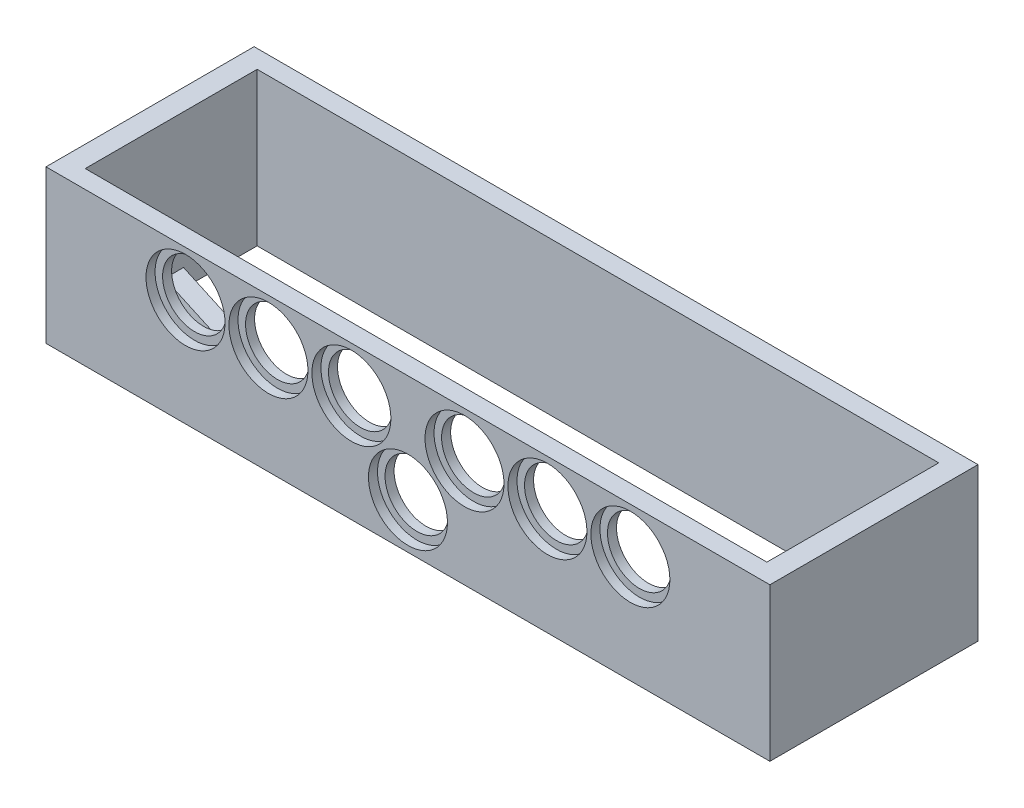
SolidWorks part; units mm, degrees
ref_plane "Přední rovina" through (0, 0, 0) normal (0, 0, 1) x (1, 0, 0)
ref_plane "Horní rovina" through (0, 0, 0) normal (0, 1, 0) x (1, 0, 0)
ref_plane "Pravá rovina" through (0, 0, 0) normal (1, 0, 0) x (0, 0, -1)
sketch "Skica1" plane through (0, 0, 0) normal (0, 1, 0) x (1, 0, 0)
  line L0 (0, 0) -> (240, 0)
  line L1 (240, 0) -> (240, 69)
  line L2 (240, 69) -> (0, 69)
  line L3 (0, 69) -> (0, 0)
  line L4 (7, 63) -> (7, 6)
  line L5 (7, 6) -> (233, 6)
  line L6 (233, 6) -> (233, 63)
  line L7 (233, 63) -> (7, 63)
  dimension "D1" = 240
  dimension "D2" = 69
  dimension "D3" = 6
  dimension "D4" = 6
  dimension "D5" = 7
  dimension "D6" = 7
extrude "Přidat vysunutím1" add sketch "Skica1" along normal blind 50.7
sketch "Skica2" plane through (0, 0, 0) normal (0, 0, 1) x (1, 0, 0)
  line L0 (0, 50.7) -> (0, 0) construction
  line L1 (0, 50.7) -> (240, 50.7) construction
  line L2 (-15.8466, 35.6) -> (273.2323, 35.6) construction
  line L3 (240, 50.7) -> (240, 0) construction
  line L4 (0, 0) -> (240, 0) construction
  circle A0 centre (46.25, 35.6) radius 13.1
  circle A1 centre (73.75, 35.6) radius 13.1
  circle A2 centre (101.25, 35.6) radius 13.1
  circle A3 centre (138.75, 35.6) radius 13.1
  circle A4 centre (166.25, 35.6) radius 13.1
  circle A5 centre (193.75, 35.6) radius 13.1
  circle A6 centre (120, 15.1) radius 13.1
  dimension "D2" = 26.2
  dimension "D9" = 26.2
  dimension "D10" = 26.2
  dimension "D11" = 26.2
  dimension "D12" = 26.2
  dimension "D13" = 26.2
  dimension "D14" = 26.2
  dimension "D1" = 46.25
  dimension "D3" = 15.1
  dimension "D4" = 27.5
  dimension "D5" = 27.5
  dimension "D6" = 27.5
  dimension "D7" = 27.5
  dimension "D8" = 46.25
  dimension "D15" = 120
  dimension "D16" = 15.1
extrude "Odebrat vysunutím1" cut sketch "Skica2" against normal blind 3
sketch "Skica4" plane through (0, 0, 0) normal (0, 0, 1) x (1, 0, 0)
  circle A0 centre (46.25, 35.6) radius 10.6
  circle A1 centre (73.75, 35.6) radius 10.6
  circle A2 centre (138.75, 35.6) radius 10.6
  circle A3 centre (101.25, 35.6) radius 10.6
  circle A4 centre (120, 15.1) radius 10.6
  circle A5 centre (166.25, 35.6) radius 10.6
  circle A6 centre (193.75, 35.6) radius 10.6
  dimension "D1" = 21.2
extrude "Odebrat vysunutím2" cut sketch "Skica4" against normal blind 6
sketch "Skica5" plane through (0, 0, 0) normal (0, -1, 0) x (1, 0, 0)
  line L1 (0, -34.5) -> (110, 0)
  line L2 (0, 0) -> (240, 0) construction
  line L3 (0, -40.79) -> (130.0551, 0)
  line L4 (240, -34.5) -> (130, 0)
  line L5 (240, 0) -> (240, -69) construction
  line L6 (240, -40.79) -> (109.9449, 0)
  line L7 (0, -40.79) -> (0, -34.5)
  line L8 (110, 0) -> (130.0551, 0)
  line L9 (130, 0) -> (109.9449, 0)
  line L10 (240, -34.5) -> (240, -40.79)
  line L11 (0, -69) -> (0, 0) construction
  line M8 (7, -63) -> (7, -6)
  line M9 (7, -6) -> (233, -6)
  line M10 (233, -6) -> (233, -63)
  dimension "D1" = 6.29
  dimension "D2" = 180
  dimension "D3" = 6.0017
  dimension "D4" = 110
  dimension "D5" = 110
  dimension "D6" = 6.29
  dimension "D7" = 180
  dimension "D8" = 6.0017
extrude "Přidat vysunutím2" add sketch "Skica5" against normal blind 6 contours L6 L4 M10 M9 | L3 L1 M8 M9
